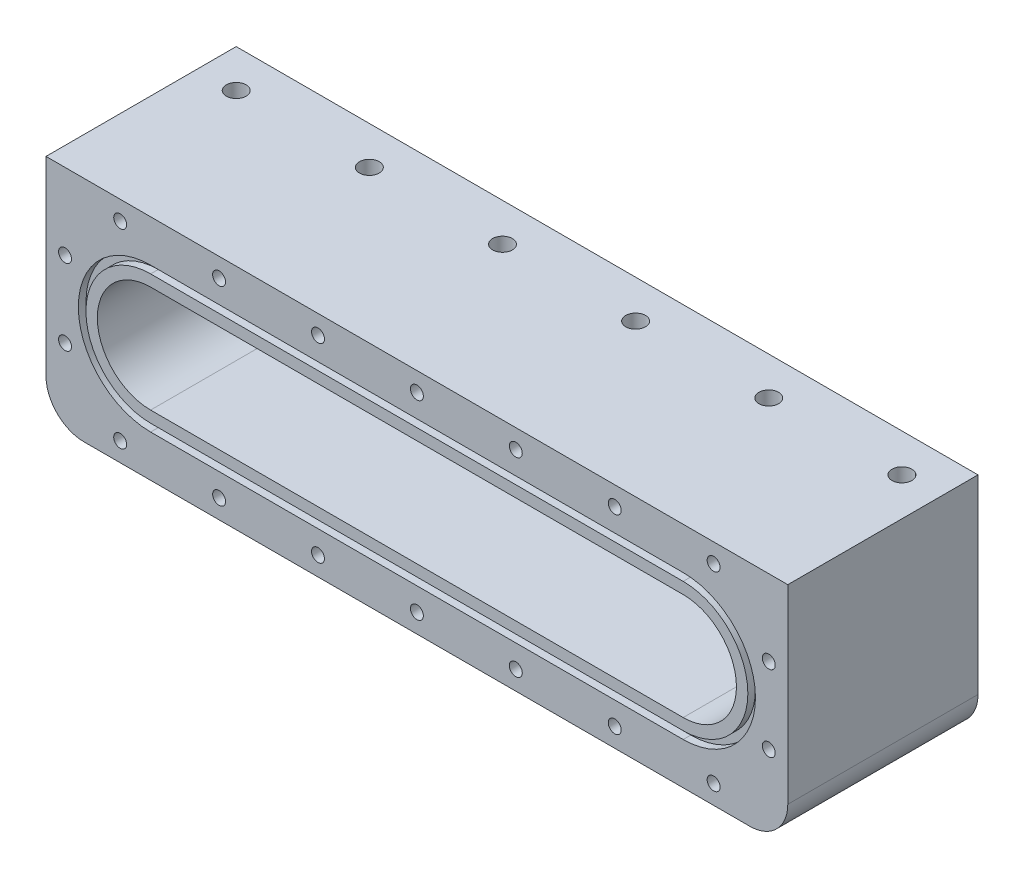
SolidWorks part; units mm, degrees
ref_plane "Front Plane" through (0, 0, 0) normal (0, 0, 1) x (1, 0, 0)
ref_plane "Top Plane" through (0, 0, 0) normal (0, 1, 0) x (1, 0, 0)
ref_plane "Right Plane" through (0, 0, 0) normal (1, 0, 0) x (0, 0, -1)
sketch "Sketch1" plane through (0, 0, 0) normal (0, 1, 0) x (1, 0, 0)
  line L1 (-123.825, 31.75) -> (123.825, 31.75)
  line L2 (-123.825, 31.75) -> (-123.825, -31.75)
  line L3 (-123.825, -31.75) -> (123.825, -31.75)
  line L4 (123.825, 31.75) -> (123.825, -31.75)
  line L5 (-123.825, 31.75) -> (123.825, -31.75) construction
  line L6 (-123.825, -31.75) -> (123.825, 31.75) construction
  point P0 (0, 0)
  dimension "D1" = 63.5
  dimension "D2" = 247.65
extrude "Boss-Extrude1" add sketch "Sketch1" along normal blind 76.2
sketch "Sketch2" plane through (0, 0, 31.75) normal (0, 0, 1) x (1, 0, 0)
  line L0 (-88.9, 38.1) -> (88.9, 38.1) construction
  line L1 (-88.9, 55.88) -> (88.9, 55.88)
  line L2 (-88.9, 20.32) -> (88.9, 20.32)
  line L3 (-123.825, 76.2) -> (-123.825, 0) construction
  arc A0 (-88.9, 55.88) -> (-88.9, 20.32) centre (-88.9, 38.1) ccw
  arc A1 (88.9, 20.32) -> (88.9, 55.88) centre (88.9, 38.1) ccw
  point P2 (0, 38.1)
  point P11 (-123.825, 38.1)
  dimension "D2" = 17.78
  dimension "D1" = 177.8
extrude "Cut-Extrude1" cut sketch "Sketch2" against normal blind 57.15
sketch "Sketch5" plane through (0, 0, 31.75) normal (0, 0, 1) x (1, 0, 0)
  line L0 (-123.825, 38.1) -> (123.825, 38.1) construction
  line L1 (-123.825, 76.2) -> (-123.825, 0) construction
  line L2 (123.825, 76.2) -> (123.825, 0) construction
  line L3 (-123.825, 69.85) -> (123.825, 69.85) construction
  line L4 (-123.825, 76.2) -> (123.825, 76.2) construction
  line L5 (0, 76.2) -> (0, 0) construction
  line L6 (-123.825, 0) -> (123.825, 0) construction
  circle A0 centre (0, 69.85) radius 2.159
  circle A1 centre (33.02, 69.85) radius 2.159
  circle A2 centre (66.04, 69.85) radius 2.159
  circle A3 centre (-66.04, 69.85) radius 2.159
  circle A4 centre (-33.02, 69.85) radius 2.159
  circle A6 centre (-99.06, 69.85) radius 2.159
  circle A7 centre (99.06, 69.85) radius 2.159
  circle A8 centre (-99.06, 6.35) radius 2.159
  circle A9 centre (-66.04, 6.35) radius 2.159
  circle A10 centre (-33.02, 6.35) radius 2.159
  circle A11 centre (0, 6.35) radius 2.159
  circle A12 centre (33.02, 6.35) radius 2.159
  circle A13 centre (66.04, 6.35) radius 2.159
  circle A14 centre (99.06, 6.35) radius 2.159
  circle A15 centre (-117.475, 50.8) radius 2.159
  circle A16 centre (117.475, 50.8) radius 2.159
  circle A17 centre (-117.475, 25.4) radius 2.159
  circle A18 centre (117.475, 25.4) radius 2.159
  dimension "D1" = 4.318
  dimension "D9" = 4.318
  dimension "D11" = 4.318
  dimension "D2" = 33.02
  dimension "D3" = 33.02
  dimension "D4" = 33.02
  dimension "D5" = 33.02
  dimension "D6" = 33.02
  dimension "D7" = 33.02
  dimension "D8" = 6.35
  dimension "D10" = 6.35
  dimension "D12" = 12.7
  dimension "D13" = 12.7
extrude "Cut-Extrude3" cut sketch "Sketch5" against normal blind 6.35
sketch "Sketch6" plane through (123.825, 0, 0) normal (1, 0, 0) x (0, 0, -1)
  line L0 (-25.4, 63.5) -> (31.75, 63.5) construction
  line L1 (31.75, 76.2) -> (31.75, 0) construction
  line L2 (0, 0) -> (0, 76.2) construction
  line L3 (-31.75, 0) -> (31.75, 0) construction
  line L4 (-31.75, 76.2) -> (31.75, 76.2) construction
  circle A0 centre (-19.05, 63.5) radius 3.2639
  circle A2 centre (19.05, 63.5) radius 3.2639
  dimension "D1" = 19.05
  dimension "D2" = 6.5278
  dimension "D3" = 12.7
extrude "Cut-Extrude4" [suppressed] cut sketch "Sketch6" against normal blind 6.35
mirror "Mirror1" [suppressed] about plane through (0, 0, 0) normal (1, 0, 0)
sketch "Sketch7" plane through (0, 0, 0) normal (0, -1, 0) x (-1, 0, 0)
  line L0 (-123.825, 31.75) -> (123.825, 31.75) construction
  line L2 (-123.825, -31.75) -> (-123.825, 31.75) construction
  circle A0 centre (-83.185, 15.24) radius 5.08
  dimension "D1" = 10.16
  dimension "D2" = 16.51
  dimension "D3" = 40.64
extrude "Cut-Extrude5" cut sketch "Sketch7" against normal blind 25.4
fillet "Fillet1" radius 12.7 2 edges at (-123.825, 0, 0) (123.825, 0, 0)
sketch "Sketch8" plane through (0, 0, 31.75) normal (0, 0, 1) x (1, 0, 0)
  line L0 (-88.9, 20.32) -> (88.9, 20.32) construction
  line L1 (88.9, 55.88) -> (-88.9, 55.88) construction
  line L2 (-88.9, 20.32) -> (88.9, 20.32)
  line L3 (88.9, 55.88) -> (-88.9, 55.88)
  line L4 (-88.9, 16.51) -> (88.9, 16.51)
  line L5 (88.9, 59.69) -> (-88.9, 59.69)
  line L6 (88.9, 62.23) -> (-88.9, 62.23)
  line L7 (-88.9, 13.97) -> (88.9, 13.97)
  arc A0 (88.9, 20.32) -> (88.9, 55.88) centre (88.9, 38.1) ccw construction
  arc A1 (-88.9, 55.88) -> (-88.9, 20.32) centre (-88.9, 38.1) ccw construction
  arc A2 (88.9, 20.32) -> (88.9, 55.88) centre (88.9, 38.1) ccw
  arc A3 (-88.9, 55.88) -> (-88.9, 20.32) centre (-88.9, 38.1) ccw
  arc A4 (-88.9, 59.69) -> (-88.9, 16.51) centre (-88.9, 38.1) ccw
  arc A5 (88.9, 16.51) -> (88.9, 59.69) centre (88.9, 38.1) ccw
  arc A6 (-88.9, 62.23) -> (-88.9, 13.97) centre (-88.9, 38.1) ccw
  arc A7 (88.9, 13.97) -> (88.9, 62.23) centre (88.9, 38.1) ccw
  dimension "D1" = 3.81
  dimension "D2" = 2.54
extrude "Cut-Extrude6" cut sketch "Sketch8" against normal blind 2.54 contours L7 A7 L6 A6 A5 L4 A4 L5
sketch "Sketch9" plane through (0, 76.2, 44.45) normal (0, -1, 0) x (-1, 0, 0)
  line L0 (-123.825, 63.5) -> (123.825, 63.5) construction
  line L4 (-123.825, 12.7) -> (-123.825, 76.2) construction
  line L5 (-123.825, 76.2) -> (123.825, 76.2) construction
  circle A0 centre (-111.125, 63.5) radius 3.302
  circle A4 centre (-66.675, 63.5) radius 3.302
  circle A5 centre (-22.225, 63.5) radius 3.302
  circle A6 centre (22.225, 63.5) radius 3.302
  circle A7 centre (66.675, 63.5) radius 3.302
  circle A8 centre (111.125, 63.5) radius 3.302
  dimension "D2" = 6.604
  dimension "D3" = 12.7
  dimension "D1" = 12.7
  dimension "D5" = 44.45
  dimension "D4" = 6
extrude "Cut-Extrude7" cut sketch "Sketch9" along normal blind 12.7
sketch "Sketch10" plane through (0, 0, 31.75) normal (0, 0, 1) x (1, 0, 0)
  line L0 (0, 76.2) -> (0, 0) construction
  line L1 (-123.825, 76.2) -> (123.825, 76.2) construction
  line L7 (-106.68, 20.32) -> (106.68, 20.32)
  line L8 (-106.68, 20.32) -> (-106.68, 55.88)
  line L9 (-106.68, 55.88) -> (106.68, 55.88)
  line L10 (106.68, 20.32) -> (106.68, 55.88)
  line L11 (-106.68, 20.32) -> (106.68, 55.88) construction
  line L12 (-106.68, 55.88) -> (106.68, 20.32) construction
  point P5 (0, 38.1)
  point P6 (0, 38.1)
